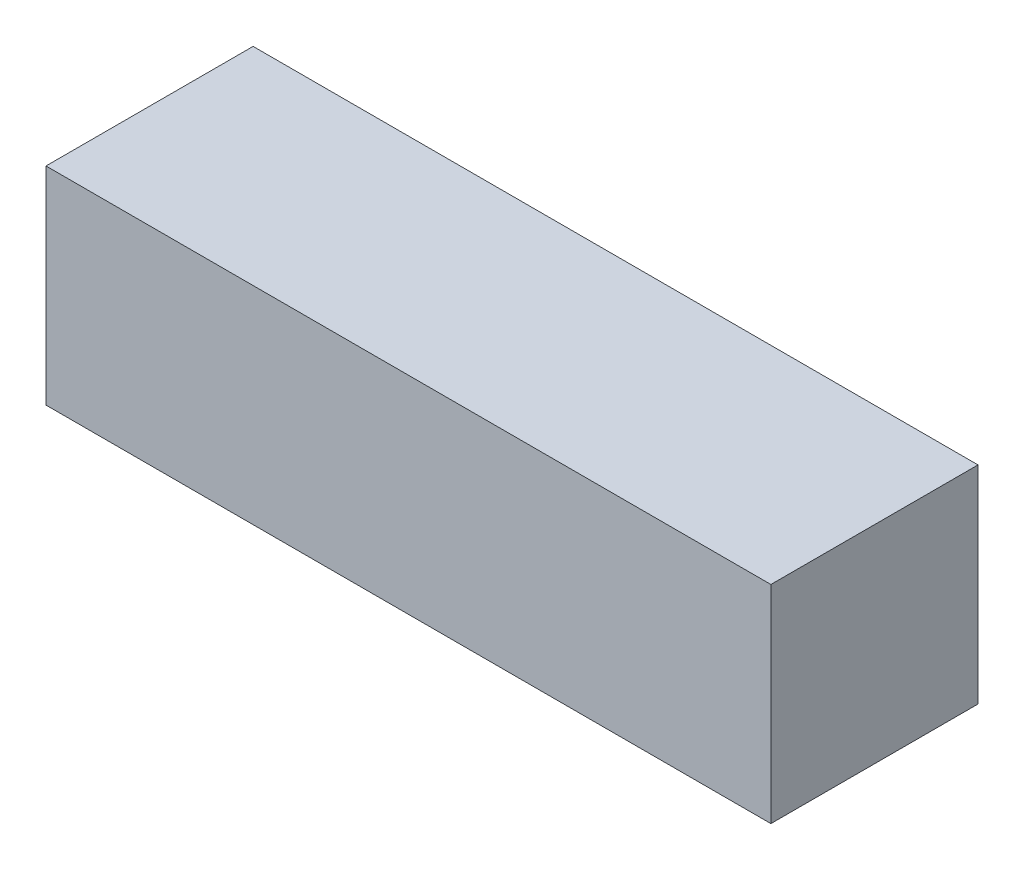
SolidWorks part; units mm, degrees
ref_plane "Спереди" through (0, 0, 0) normal (0, 0, 1) x (1, 0, 0)
ref_plane "Сверху" through (0, 0, 0) normal (0, 1, 0) x (1, 0, 0)
ref_plane "Справа" through (0, 0, 0) normal (1, 0, 0) x (0, 0, -1)
sketch "Эскиз1" plane through (0, 0, 0) normal (1, 0, 0) x (0, 0, -1)
  line L1 (0, 0) -> (10, 0)
  line L2 (0, 0) -> (0, 10)
  line L3 (0, 10) -> (10, 10)
  line L4 (10, 0) -> (10, 10)
extrude "Бобышка-Вытянуть1" add sketch "Эскиз1" along normal blind 35
